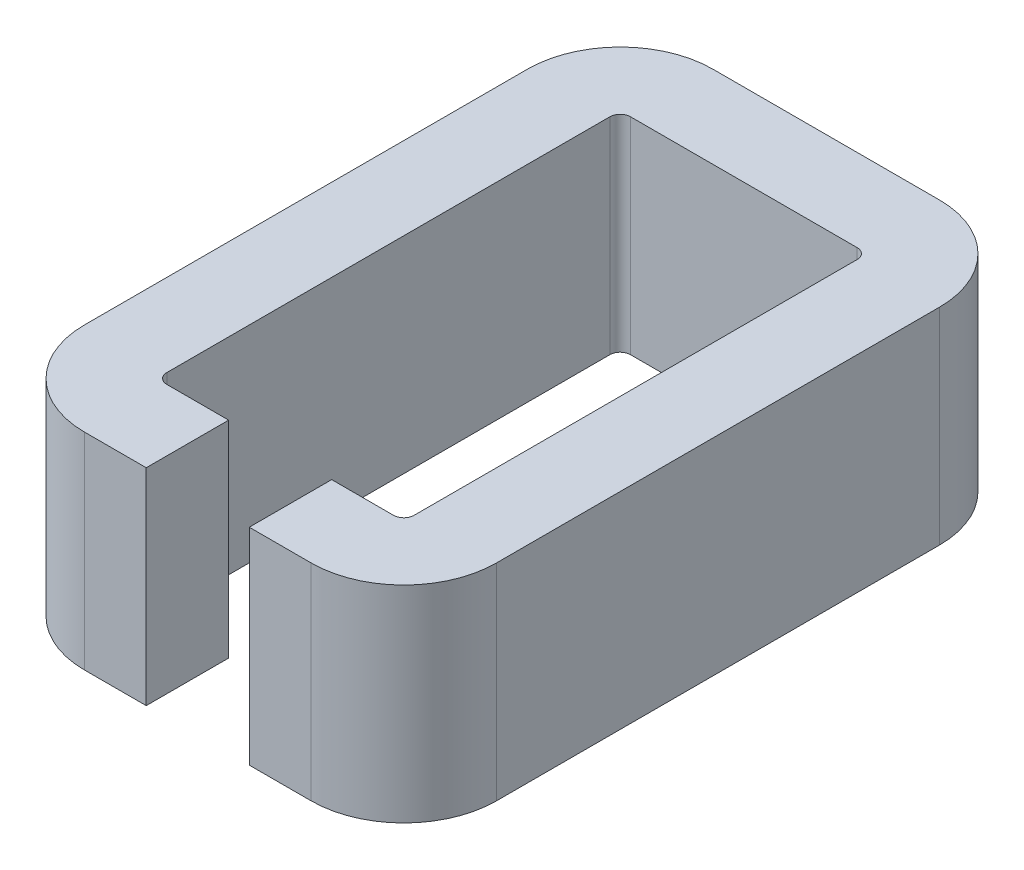
SolidWorks part; units mm, degrees
ref_plane "Front Plane" through (0, 0, 0) normal (0, 0, 1) x (1, 0, 0)
ref_plane "Top Plane" through (0, 0, 0) normal (0, 1, 0) x (1, 0, 0)
ref_plane "Right Plane" through (0, 0, 0) normal (1, 0, 0) x (0, 0, -1)
sketch "Sketch1" plane through (0, 0, 0) normal (0, 1, 0) x (1, 0, 0)
  line L0 (-4, -0.5) -> (-4, -22)
  line L1 (0.5, 0) -> (11.5, 0)
  line L2 (0, -0.5) -> (0, -22)
  line L3 (0.5, -22.5) -> (3.5, -22.5)
  line L4 (12, -0.5) -> (12, -22)
  line L5 (0.5, -26.5) -> (3.5, -26.5)
  line L6 (16, -0.5) -> (16, -22)
  line L7 (0.5, 4) -> (11.5, 4)
  line L8 (3.5, -22.5) -> (3.5, -26.5)
  line L9 (8.5, -22.5) -> (8.5, -26.5)
  line L10 (8.5, -22.5) -> (11.5, -22.5)
  line L11 (8.5, -26.5) -> (11.5, -26.5)
  line L12 (0.5, -22.5) -> (11.5, -22.5) construction
  line L14 (0.5, -26.5) -> (11.5, -26.5) construction
  arc A0 (12, -22) -> (11.5, -22.5) centre (11.5, -22) cw
  arc A1 (0.5, -22.5) -> (0, -22) centre (0.5, -22) cw
  arc A2 (0.5, 0) -> (0, -0.5) centre (0.5, -0.5) ccw
  arc A3 (12, -0.5) -> (11.5, 0) centre (11.5, -0.5) ccw
  arc A4 (0.5, -26.5) -> (-4, -22) centre (0.5, -22) cw
  arc A5 (16, -22) -> (11.5, -26.5) centre (11.5, -22) cw
  arc A6 (16, -0.5) -> (11.5, 4) centre (11.5, -0.5) ccw
  arc A7 (0.5, 4) -> (-4, -0.5) centre (0.5, -0.5) ccw
  point P7 (12, -22.5)
  point P12 (0, 0)
  point P15 (12, 0)
  dimension "D3" = 0.5
  dimension "D1" = 12
  dimension "D2" = 22.5
  dimension "D5" = 5
  dimension "D4" = 4
extrude "Boss-Extrude1" add sketch "Sketch1" along normal blind 10
